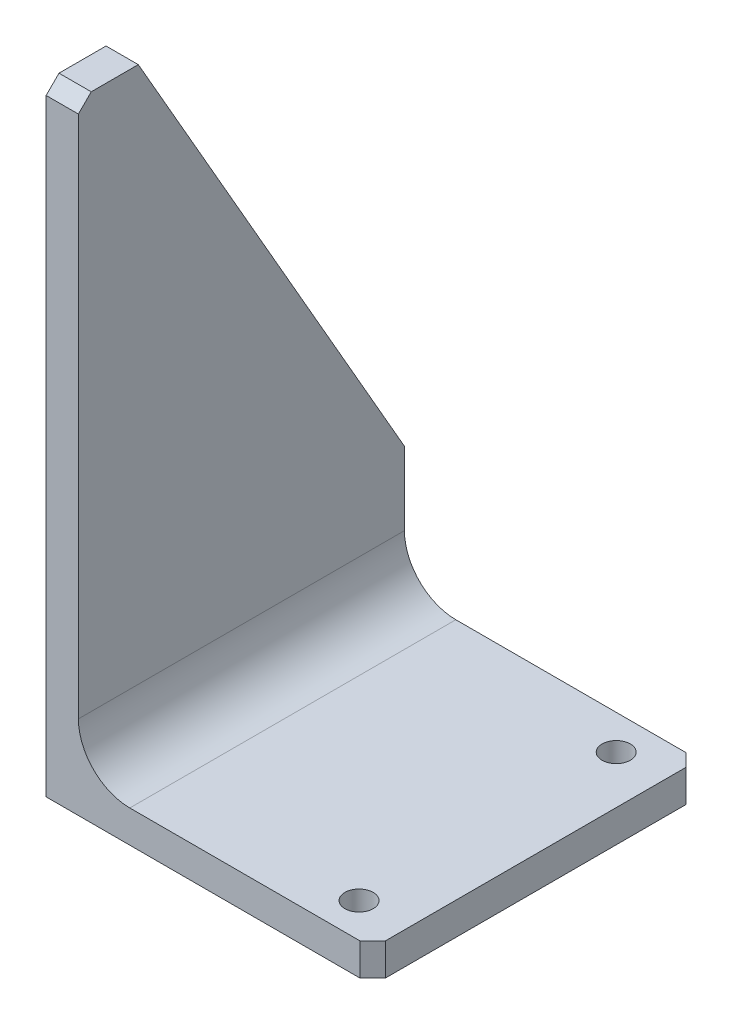
SolidWorks part; units mm, degrees
ref_plane "Plano frontal" through (0, 0, 0) normal (0, 0, 1) x (1, 0, 0)
ref_plane "Plano superior" through (0, 0, 0) normal (0, 1, 0) x (1, 0, 0)
ref_plane "Plano direito" through (0, 0, 0) normal (1, 0, 0) x (0, 0, -1)
sketch "Esboço1" plane through (0, 0, 0) normal (0, 1, 0) x (1, 0, 0)
  line L1 (31.74, -31.7) -> (-31.74, -31.7)
  line L2 (31.74, -31.7) -> (31.74, 31.7)
  line L3 (31.74, 31.7) -> (-31.74, 31.7)
  line L4 (-31.74, -31.7) -> (-31.74, 31.7)
  line L5 (31.74, -31.7) -> (-31.74, 31.7) construction
  line L6 (31.74, 31.7) -> (-31.74, -31.7) construction
  point P0 (0, 0)
  dimension "D1" = 63.48
  dimension "D2" = 63.4
extrude "Ressalto-extrusão1" add sketch "Esboço1" along normal blind 6.27
chamfer "Chanfro1" distance 2.5 angle 45 2 edges at (31.74, 3.135, 31.7) (31.74, 3.135, -31.7)
ref_plane "Plano2" through (-25.49, 0, 0) normal (-1, 0, 0) x (0, 0, 1)
sketch "Esboço2" plane through (-25.49, 0, 0) normal (-1, 0, 0) x (0, 0, 1)
  line L0 (-31.7, 30.5) -> (-31.7, 0)
  line L1 (-31.7, 0) -> (31.7, 0)
  line L4 (31.7, 0) -> (31.7, 30.5)
  line L5 (31.7, 0) -> (31.7, 30.5) construction
  line L7 (31.7, 120.63) -> (20.05, 120.63)
  line L9 (-31.7, 30.5) -> (20.05, 120.63)
  line L10 (31.7, 120.63) -> (31.7, 30.5)
extrude "Ressalto-extrusão2" add sketch "Esboço2" along normal blind 6.27
chamfer "Chanfro2" distance 2.5 angle 45 1 edges at (-28.625, 120.63, 31.7)
fillet "Filete1" radius 10 1 edges at (-25.49, 6.27, 0)
sketch "Esboço3" plane through (0, 0, 0) normal (0, -1, 0) x (-1, 0, 0)
  line L0 (-27.4814, -31.2682) -> (-29.24, -31.7) construction
  line L1 (-31.74, -29.2) -> (-31.74, 29.2) construction
  line L2 (-22.39, 0) -> (-17.3478, 0) construction
  line L3 (-22.39, 0) -> (-22.39, -25) construction
  line L4 (-22.39, 0) -> (-22.39, 25) construction
  circle A0 centre (-22.39, -25) radius 2.75
  circle A1 centre (-22.39, 25) radius 2.75
  dimension "D1" = 9.35
extrude "Corte-extrusão1" cut sketch "Esboço3" against normal blind 6.27
